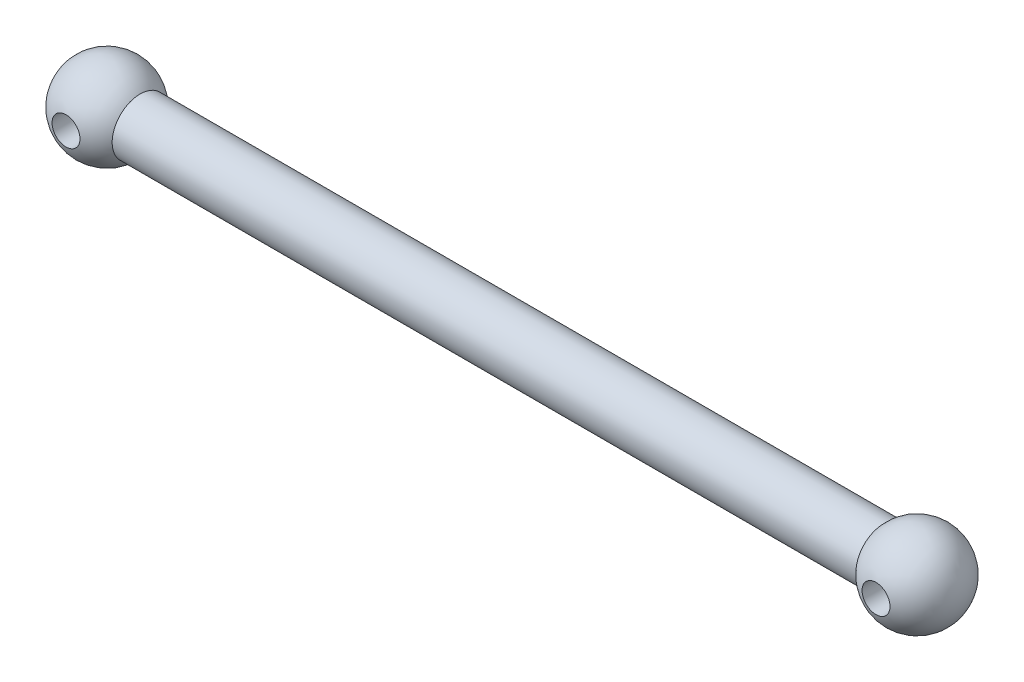
SolidWorks part; units mm, degrees
ref_plane "Front Plane" through (0, 0, 0) normal (0, 0, 1) x (1, 0, 0)
ref_plane "Top Plane" through (0, 0, 0) normal (0, 1, 0) x (1, 0, 0)
ref_plane "Right Plane" through (0, 0, 0) normal (1, 0, 0) x (0, 0, -1)
sketch "Sketch1" plane through (0, 0, 0) normal (0, 1, 0) x (1, 0, 0)
  line L0 (-26.6315, 2) -> (26.6315, 2)
  line L1 (-29, 0) -> (29, 0) construction
  line L2 (-26.6315, -2) -> (26.6315, -2)
  line L3 (-25.9, 0) -> (-32.1, 0)
  line L4 (25.9, 0) -> (32.1, 0)
  circle A0 centre (-29, 0) radius 3.1
  circle A1 centre (29, 0) radius 3.1
  point P13 (0, 0)
  dimension "D1" = 6.2
  dimension "D2" = 2
  dimension "D3" = 2
  dimension "D4" = 58
revolve "Revolve2" add sketch "Sketch1" angle 360 about L1
sketch "Sketch2" plane through (0, 0, 0) normal (0, 0, 1) x (1, 0, 0)
  line L0 (0, -3.41) -> (0, 3.41) construction
  circle A2 centre (29, 0) radius 1
  circle A3 centre (-29, 0) radius 1
  dimension "D1" = 2
  dimension "D2" = 29
extrude "Cut-Extrude1" cut sketch "Sketch2" against normal through all both and the other way through all
